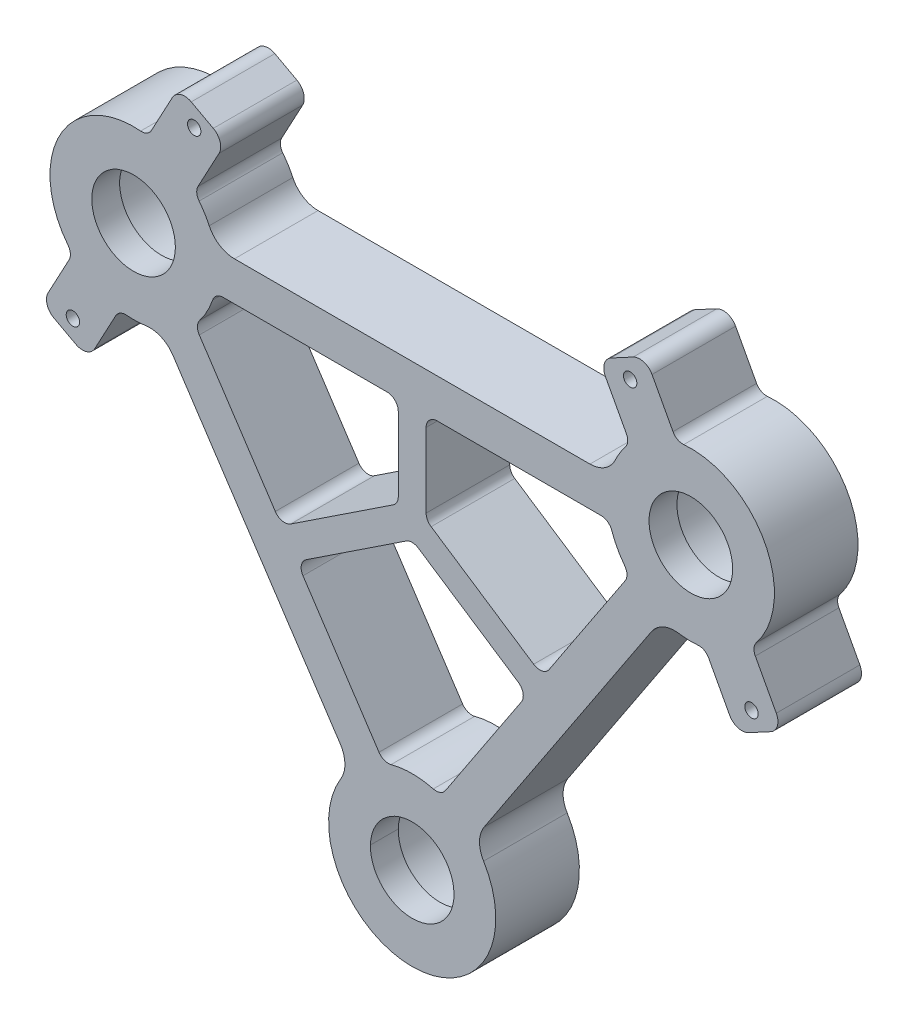
SolidWorks part; units mm, degrees
material "ABS"
ref_plane "Front Plane" through (0, 0, 0) normal (0, 0, 1) x (1, 0, 0)
ref_plane "Top Plane" through (0, 0, 0) normal (0, 1, 0) x (1, 0, 0)
ref_plane "Right Plane" through (0, 0, 0) normal (1, 0, 0) x (0, 0, -1)
sketch "Sketch1" plane through (0, 0, 0) normal (0, 0, 1) x (1, 0, 0)
  line L0 (-50, 0) -> (50, 0) construction
  line L1 (39.0316, -10.232) -> (23.461, -33.7605)
  line L2 (0, -75.5537) -> (-50, 0) construction
  line L3 (0, -75.5537) -> (50, 0) construction
  line L4 (10.9684, -65.3217) -> (44.8691, -14.0952)
  line L5 (-25, -37.7768) -> (0, -21.2323) construction
  line L6 (-35.414, -3.5) -> (-2.5, -3.5)
  line L7 (0, -21.2323) -> (25, -37.7768) construction
  line L8 (-35.414, 3.5) -> (35.414, 3.5)
  line L9 (0, -21.2323) -> (0, 0) construction
  line L10 (-39.0316, -10.232) -> (-23.461, -33.7605)
  line L11 (-44.8691, -14.0952) -> (-10.9684, -65.3217)
  line L12 (-23.461, -33.7605) -> (-2.5, -19.8889)
  line L13 (-2.5, -19.8889) -> (-2.5, -3.5)
  line L14 (2.5, -3.5) -> (2.5, -19.8889)
  line L15 (2.5, -19.8889) -> (23.461, -33.7605)
  line L16 (-20.7016, -37.9301) -> (0, -24.2302)
  line L17 (0, -24.2302) -> (20.7016, -37.9301)
  line L18 (2.5, -3.5) -> (35.414, -3.5)
  line L19 (-20.7016, -37.9301) -> (-5.1309, -61.4585)
  line L20 (20.7016, -37.9301) -> (5.1309, -61.4585)
  line L21 (36.7869, -7.1003) -> (63.2131, 7.1003) construction
  line L22 (-36.7869, -7.1003) -> (-63.2131, 7.1003) construction
  line L23 (42.8997, 13.2131) -> (57.1003, -13.2131) construction
  line L24 (-57.1003, -13.2131) -> (-42.8997, 13.2131) construction
  line L25 (39.081, 10.2847) -> (34.6684, 18.4962)
  line L26 (35.6872, 21.8817) -> (39.6512, 24.0118)
  line L27 (43.0367, 22.993) -> (47.4493, 14.7815)
  line L28 (52.5507, -14.7815) -> (56.9633, -22.993)
  line L29 (60.3488, -24.0118) -> (64.3128, -21.8817)
  line L30 (65.3316, -18.4962) -> (60.919, -10.2847)
  line L31 (-39.081, 10.2847) -> (-34.6684, 18.4962)
  line L32 (-35.6872, 21.8817) -> (-39.6512, 24.0118)
  line L33 (-43.0367, 22.993) -> (-47.4493, 14.7815)
  line L34 (-52.5507, -14.7815) -> (-56.9633, -22.993)
  line L35 (-60.3488, -24.0118) -> (-64.3128, -21.8817)
  line L36 (-65.3316, -18.4962) -> (-60.919, -10.2847)
  arc A0 (-39.0316, -10.232) -> (-35.414, -3.5) centre (-50, 0) ccw
  arc A1 (35.414, -3.5) -> (39.0316, -10.232) centre (50, 0) ccw
  arc A2 (5.1309, -61.4585) -> (-5.1309, -61.4585) centre (0, -75.5537) ccw
  arc A3 (-35.414, 3.5) -> (-39.081, 10.2847) centre (-50, 0) ccw
  arc A4 (44.8691, -14.0952) -> (52.5507, -14.7815) centre (50, 0) ccw
  arc A5 (-10.9684, -65.3217) -> (10.9684, -65.3217) centre (0, -75.5537) ccw
  arc A6 (39.081, 10.2847) -> (35.414, 3.5) centre (50, 0) ccw
  arc A7 (60.919, -10.2847) -> (47.4493, 14.7815) centre (50, 0) ccw
  circle A8 centre (50, 0) radius 15 construction
  arc A9 (64.3128, -21.8817) -> (65.3316, -18.4962) centre (63.1294, -19.6795) ccw
  arc A10 (56.9633, -22.993) -> (60.3488, -24.0118) centre (59.1655, -21.8096) ccw
  arc A11 (34.6684, 18.4962) -> (35.6872, 21.8817) centre (36.8706, 19.6795) cw
  arc A12 (39.6512, 24.0118) -> (43.0367, 22.993) centre (40.8345, 21.8096) cw
  arc A13 (-47.4493, 14.7815) -> (-60.919, -10.2847) centre (-50, 0) ccw
  arc A14 (-52.5507, -14.7815) -> (-44.8691, -14.0952) centre (-50, 0) ccw
  arc A15 (-56.9633, -22.993) -> (-60.3488, -24.0118) centre (-59.1655, -21.8096) cw
  arc A16 (-64.3128, -21.8817) -> (-65.3316, -18.4962) centre (-63.1294, -19.6795) cw
  arc A17 (-34.6684, 18.4962) -> (-35.6872, 21.8817) centre (-36.8706, 19.6795) ccw
  arc A18 (-39.6512, 24.0118) -> (-43.0367, 22.993) centre (-40.8345, 21.8096) ccw
  circle A19 centre (-50, 0) radius 15 construction
  point P3 (0, 0)
  point P69 (-33.485, 20.6983)
  point P72 (-41.8533, 25.1952)
  dimension "D4" = 30
  dimension "D5" = 30
  dimension "D6" = 30
  dimension "D14" = 2.5
  dimension "D17" = 2.5
  dimension "D1" = 100
  dimension "D2" = 90.6
  dimension "D3" = 7
  dimension "D7" = 7
  dimension "D8" = 7
  dimension "D9" = 5
  dimension "D10" = 5
  dimension "D11" = 5
  dimension "D12" = 9.5
  dimension "D13" = 52.1
  dimension "D15" = 9.5
  dimension "D16" = 52.1
extrude "Boss-Extrude1" add sketch "Sketch1" along normal mid plane 15
ref_axis "Axis1" through (0, -75.5537, 7.5) along (0, 0, -1)
ref_axis "Axis2" through (50, 0, 7.5) along (0, 0, -1)
ref_axis "Axis3" through (-50, 0, 7.5) along (0, 0, -1)
fillet "Fillet1" radius 2 23 edges at (5.1309, -61.4585, 0) (-35.414, -3.5, 0) (-39.0316, -10.232, 0) (-5.1309, -61.4585, 0) (39.0316, -10.232, 0) (35.414, -3.5, 0) (-2.5, -3.5, 0) (-23.461, -33.7605, 0) (-20.7016, -37.9301, 0) (20.7016, -37.9301, 0) (2.5, -3.5, 0) (23.461, -33.7605, 0) (-2.5, -19.8889, 0) (0, -24.2302, 0) (2.5, -19.8889, 0) (39.081, 10.2847, 0) (47.4493, 14.7815, 0) (60.919, -10.2847, 0) (52.5507, -14.7815, 0) (-60.919, -10.2847, 0) (-47.4493, 14.7815, 0) (-39.081, 10.2847, 0) (-52.5507, -14.7815, 0)
fillet "Fillet2" radius 5 6 edges at (-35.414, 3.5, 0) (44.8691, -14.0952, 0) (10.9684, -65.3217, 0) (-10.9684, -65.3217, 0) (35.414, 3.5, 0) (-44.8691, -14.0952, 0)
ref_plane "Plane1" through (50, 0, 0) normal (1, 0, 0) x (0, 0, -1)
ref_plane "Plane2" through (-50, 0, 0) normal (1, 0, 0) x (0, 0, -1)
sketch "Sketch6" plane through (-50, 0, 0) normal (1, 0, 0) x (0, 0, -1)
  line L0 (-7.5, 0) -> (-7.5, 7.5)
  line L1 (-7.5, -14.8412) -> (-7.5, -15) construction
  line L6 (-2.5, 9.5) -> (7.5, 9.5)
  line L8 (-7.5, 0) -> (7.5, 0) construction
  line L9 (7.5, 0) -> (-7.5, 0)
  line L10 (-2.5, 9.5) -> (-2.5, 7.5)
  line L11 (-2.5, 7.5) -> (-7.5, 7.5)
  line L12 (7.5, 0) -> (7.5, 9.5)
  line L13 (7.5, -15) -> (7.5, -14.8412) construction
  dimension "D1" = 7.5
  dimension "D2" = 9.5
  dimension "D3" = 5
revolve "Cut-Revolve1" cut sketch "Sketch6" angle 360 about axis through (-50, 0, 7.5) along (0, 0, -1)
sketch "Sketch7" plane through (50, 0, 0) normal (1, 0, 0) x (0, 0, -1)
  line L10 (7.5, 0) -> (-7.5, 0)
  line L11 (-7.5, 0) -> (7.5, 0) construction
  line L12 (-7.5, 0) -> (-7.5, 7.5)
  line L13 (-7.5, -14.8412) -> (-7.5, -15) construction
  line L14 (-7.5, 7.5) -> (-2.5, 7.5)
  line L15 (-2.5, 7.5) -> (-2.5, 9.5)
  line L16 (-2.5, 9.5) -> (7.5, 9.5)
  line L17 (7.5, -15) -> (7.5, -14.8412) construction
  line L18 (7.5, 9.5) -> (7.5, 0)
  dimension "D1" = 9.5
  dimension "D2" = 7.5
  dimension "D3" = 5
revolve "Cut-Revolve2" cut sketch "Sketch7" angle 360 about axis through (50, 0, 7.5) along (0, 0, -1)
sketch "Sketch8" plane through (0, 0, 0) normal (1, 0, 0) x (0, 0, -1)
  line L10 (7.5, -75.5537) -> (-15.0022, -75.5537)
  line L11 (-7.5, -75.5537) -> (7.5, -75.5537) construction
  line L12 (-15.0022, -75.5537) -> (-7.5, -83.0537)
  line L13 (-7.5, -67.7489) -> (-7.5, -90.5537) construction
  line L14 (-7.5, -83.0537) -> (-2.5, -83.0537)
  line L15 (-2.5, -83.0537) -> (-2.5, -85.0537)
  line L16 (-2.5, -85.0537) -> (7.5, -85.0537)
  line L17 (7.5, -90.5537) -> (7.5, -67.7489) construction
  line L18 (7.5, -85.0537) -> (7.5, -75.5537)
  dimension "D1" = 7.5
  dimension "D2" = 9.5
  dimension "D3" = 5
revolve "Cut-Revolve3" cut sketch "Sketch8" angle 360 about axis through (0, -75.5537, 7.5) along (0, 0, -1)
chamfer "Chamfer1" distance 1 angle 45 3 edges at (9.5, -75.5537, -7.5) (-40.5, 0, -7.5) (59.5, 0, -7.5)
sketch "Sketch9" plane through (0, 0, 0) normal (1, 0, 0) x (0, 0, -1)
  line L1 (-7.5, -75.3962) -> (7.5, -75.3962)
  line L2 (-7.5, -67.7489) -> (-7.5, -90.5537) construction
  line L3 (7.5, -90.5537) -> (7.5, -67.7489) construction
split line "Split Line1"
ref_point "Point1"
hole_wizard "M2.5 Tapped Hole1" positions "Sketch11" profile "Sketch12" tap size "M2.5" standard "ISO" end condition through all
sketch "Sketch11" plane through (0, 0, -7.5) normal (0, 0, -1) x (-1, 0, 0)
  line L0 (-39.1129, 20.2601) -> (-60.8871, -20.2601) construction
  line L2 (-46.7987, 15.9922) -> (-43.0367, 22.993) construction
  line L5 (-34.6684, 18.4962) -> (-38.4304, 11.4954) construction
  line L6 (39.1129, 20.2601) -> (60.8871, -20.2601) construction
  line L8 (38.4304, 11.4954) -> (34.6684, 18.4962) construction
  line L9 (43.0367, 22.993) -> (46.7987, 15.9922) construction
  circle A0 centre (-50, 0) radius 10.5 construction
  circle A1 centre (50, 0) radius 10.5 construction
  point P0 (-39.1129, 20.2601)
  point P2 (-60.8871, -20.2601)
  point P20 (-50, 0)
  point P24 (39.1129, 20.2601)
  point P26 (60.8871, -20.2601)
  point P38 (50, 0)
  dimension "D1" = 46
  dimension "D2" = 46
sketch "Sketch12" plane through (39.1129, 20.2601, -7.5) normal (1, 0, 0) x (0, 1, 0)
  line L0 (0, 0) -> (0, 15)
  line L1 (0, 15) -> (1.2, 15)
  line L2 (1.2, 15) -> (1.2, 0.3)
  line L3 (1.2, 0.3) -> (1.5, 0)
  line L5 (1.5, 0) -> (0, 0)
  line L6 (-1.2, 0.3) -> (-1.5, 0) construction
  line L11 (0, -6.35) -> (0, 107.95) construction
  dimension "Thru Tap Drill Dia." = 2.4
  dimension "Thru Tap Drill Depth" = 15
  dimension "Near C'Sink Dia." = 3
  dimension "Near C'Sink Angle" = 90
cosmetic thread "Hole Thread3" parameters "D2"=2.5
cosmetic thread "Hole Thread4" parameters "D2"=2.5
cosmetic thread "Hole Thread5" parameters "D2"=2.5
cosmetic thread "Hole Thread6" parameters "D2"=2.5
